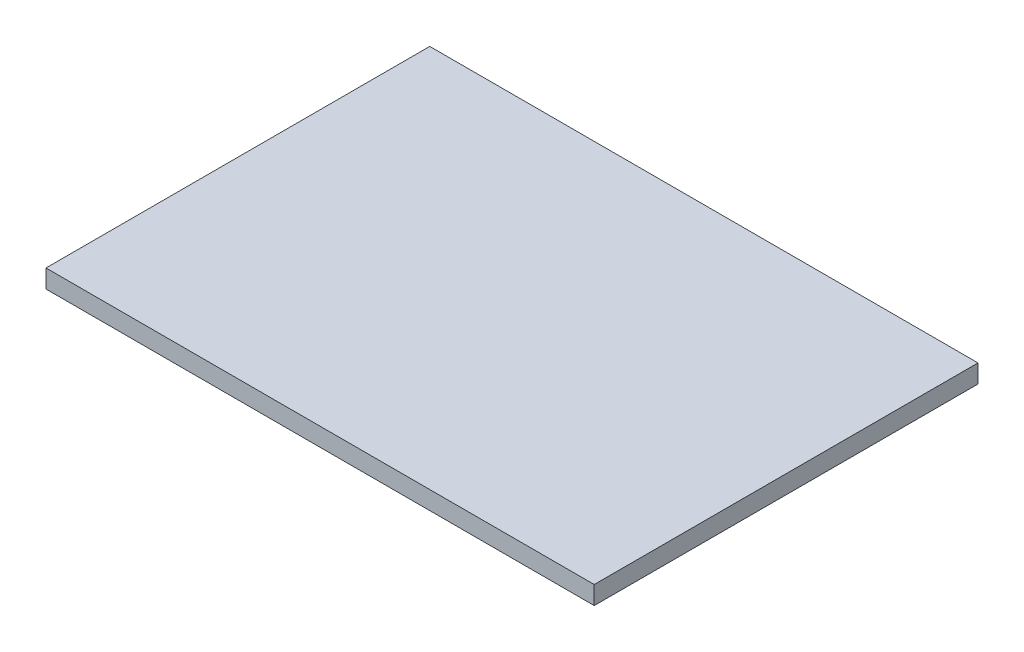
SolidWorks part; units mm, degrees
ref_plane "Front Plane" through (0, 0, 0) normal (0, 0, 1) x (1, 0, 0)
ref_plane "Top Plane" through (0, 0, 0) normal (0, 1, 0) x (1, 0, 0)
ref_plane "Right Plane" through (0, 0, 0) normal (1, 0, 0) x (0, 0, -1)
sketch "Sketch1" plane through (0, 0, 0) normal (0, 1, 0) x (1, 0, 0)
  line L1 (-13.3, 12.6) -> (16.7, 12.6)
  line L2 (-13.3, 12.6) -> (-13.3, -8.4)
  line L3 (-13.3, -8.4) -> (16.7, -8.4)
  line L4 (16.7, 12.6) -> (16.7, -8.4)
  line L5 (-13.3, 12.6) -> (16.7, -8.4) construction
  line L6 (-13.3, -8.4) -> (16.7, 12.6) construction
  point P4 (1.7, 2.1)
  dimension "D1" = 21
  dimension "D2" = 30
extrude "Boss-Extrude1" add sketch "Sketch1" along normal blind 1
